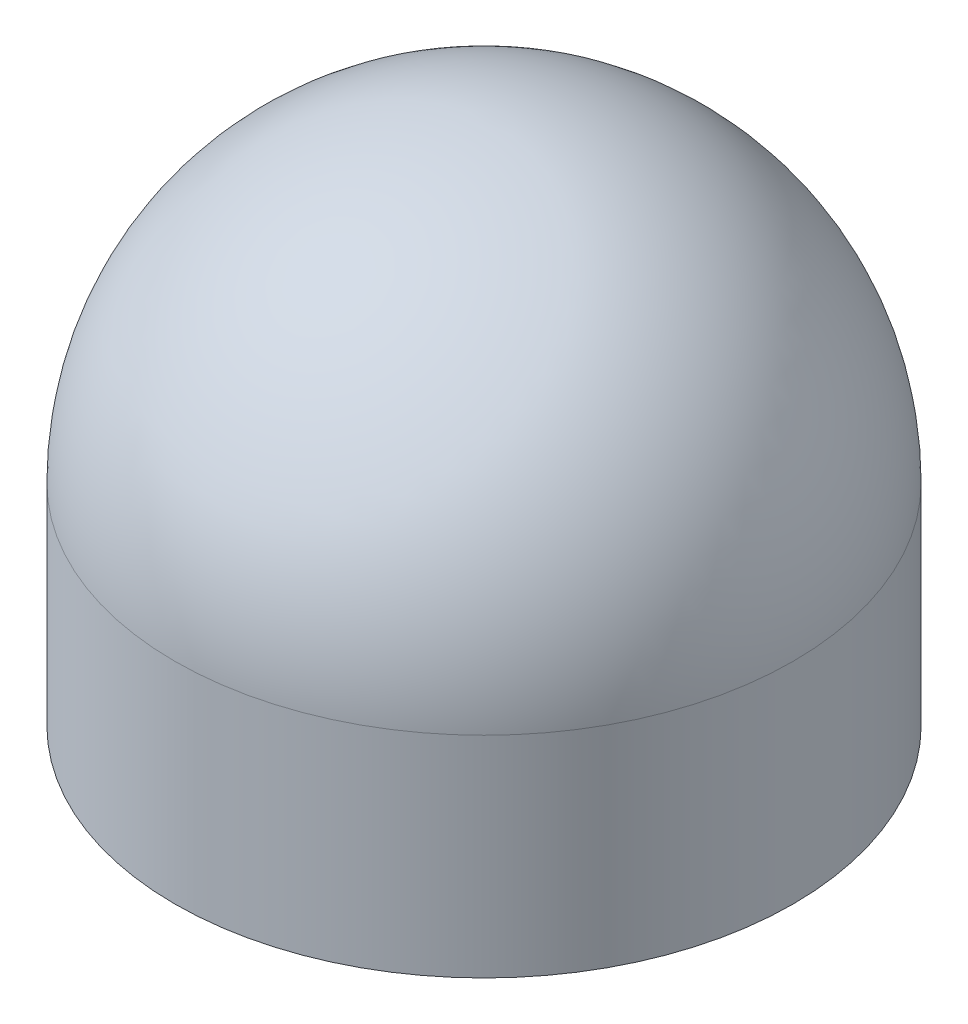
SolidWorks part; units mm, degrees
ref_plane "Front Plane" through (0, 0, 0) normal (0, 0, 1) x (1, 0, 0)
ref_plane "Top Plane" through (0, 0, 0) normal (0, 1, 0) x (1, 0, 0)
ref_plane "Right Plane" through (0, 0, 0) normal (1, 0, 0) x (0, 0, -1)
sketch "Sketch1" plane through (0, 0, 0) normal (0, 1, 0) x (1, 0, 0)
  circle A0 centre (0, 0) radius 7.5
  dimension "D1" = 15
extrude "Boss-Extrude1" add sketch "Sketch1" along normal blind 12.6
fillet "Fillet1" radius 7.5 1 edges at (0, 12.6, 7.5)
sketch "Sketch2" plane through (0, 0, 0) normal (0, -1, 0) x (1, 0, 0)
  circle A0 centre (0, 0) radius 1.625
  dimension "D1" = 3.25
extrude "Cut-Extrude1" cut sketch "Sketch2" against normal blind 12
